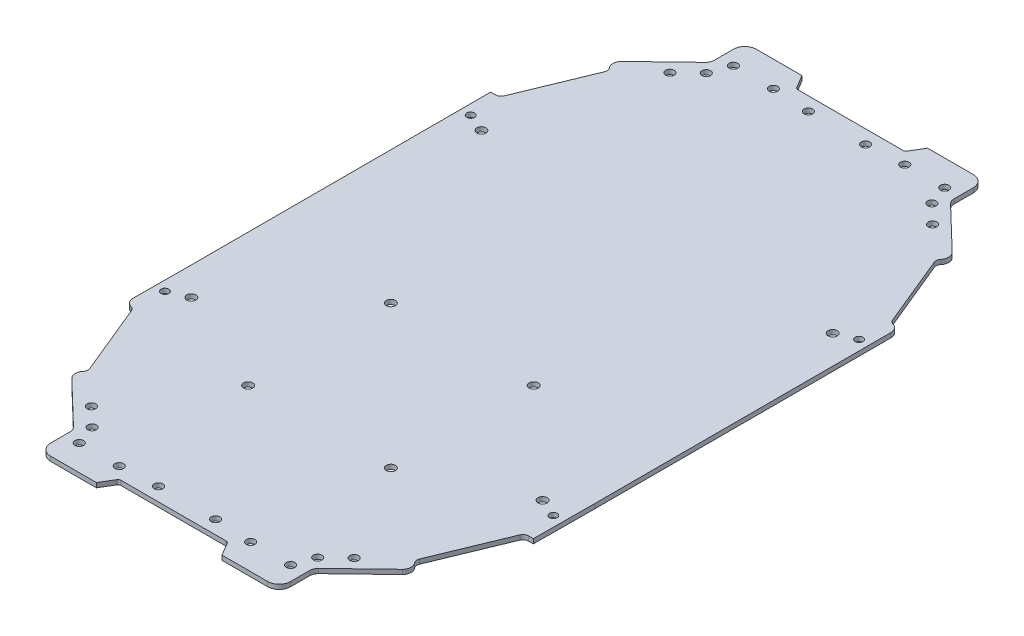
SolidWorks part; units mm, degrees
ref_plane "Front Plane" through (0, 0, 0) normal (0, 0, 1) x (1, 0, 0)
ref_plane "Top Plane" through (0, 0, 0) normal (0, 1, 0) x (1, 0, 0)
ref_plane "Right Plane" through (0, 0, 0) normal (1, 0, 0) x (0, 0, -1)
ref_plane "Plane1"
sketch "Sketch1" plane through (0, 0, 0) normal (0, 1, 0) x (-1, 0, 0)
  line L0 (59.7752, 259.0599) -> (56.7752, 264.0599)
  line L1 (56.7752, 264.0599) -> (36.7752, 264.0599)
  line L2 (36.7752, 264.0599) -> (36.7752, 252.0599)
  line L3 (36.7752, 252.0599) -> (18.7553, 234.7311)
  line L4 (18.7553, 234.7311) -> (21.5279, 231.8479)
  line L5 (21.5279, 231.8479) -> (10.2752, 204.5599)
  line L6 (10.2752, 204.5599) -> (7.2711, 204.5599)
  line L7 (7.2711, 204.5599) -> (7.1571, 183.0599)
  line L8 (7.1571, 183.0599) -> (7.1571, 76.6124)
  line L9 (7.1571, 76.6124) -> (10.1571, 76.6124)
  line L10 (10.1571, 76.6124) -> (21.4099, 49.3243)
  line L11 (21.4099, 49.3243) -> (18.6373, 46.4412)
  line L12 (18.6373, 46.4412) -> (36.6571, 29.1124)
  line L13 (36.6571, 29.1124) -> (36.6571, 17.1124)
  line L14 (36.6571, 17.1124) -> (56.6571, 17.1124)
  line L15 (56.6571, 17.1124) -> (59.6571, 22.1124)
  line L16 (59.6571, 22.1124) -> (78.6571, 22.1124)
  line L17 (78.6571, 22.1124) -> (97.6571, 22.1124)
  line L18 (97.6571, 22.1124) -> (100.6571, 17.1124)
  line L19 (100.6571, 17.1124) -> (120.6571, 17.1124)
  line L20 (120.6571, 17.1124) -> (120.6571, 29.1124)
  line L21 (120.6571, 29.1124) -> (138.677, 46.4412)
  line L22 (138.677, 46.4412) -> (135.9044, 49.3243)
  line L23 (135.9044, 49.3243) -> (147.1571, 76.6124)
  line L24 (147.1571, 76.6124) -> (150.1571, 76.6124)
  line L25 (150.1571, 76.6124) -> (150.1571, 183.0599)
  line L26 (150.1571, 183.0599) -> (150.2752, 204.5599)
  line L27 (150.2752, 204.5599) -> (147.2752, 204.5599)
  line L28 (147.2752, 204.5599) -> (136.0224, 231.8479)
  line L29 (136.0224, 231.8479) -> (138.795, 234.7311)
  line L30 (138.795, 234.7311) -> (120.7752, 252.0599)
  line L31 (120.7752, 252.0599) -> (120.7752, 264.0599)
  line L32 (120.7752, 264.0599) -> (100.7752, 264.0599)
  line L33 (100.7752, 264.0599) -> (97.7752, 259.0599)
  line L34 (97.7752, 259.0599) -> (78.6571, 259.0599)
  line L35 (78.6571, 259.0599) -> (59.7752, 259.0599)
  line L38 (78.6571, 259.0599) -> (78.6571, 22.1124) construction
  line L39 (150.1571, 183.0599) -> (7.1571, 183.0599) construction
  line L85 (91.8838, 199.6325) -> (91.9874, 199.5289)
  line L87 (95.3777, 196.1387) -> (95.4193, 196.097)
  circle A0 centre (55.6571, 26.1124) radius 1.5
  circle A1 centre (39.1571, 33.1124) radius 1.5
  circle A2 centre (53.6571, 208.0599) radius 1.6
  circle A3 centre (53.6571, 158.0599) radius 1.6
  circle A4 centre (17.1571, 89.8624) radius 1.6
  circle A5 centre (103.6571, 158.0599) radius 1.6
  circle A22 centre (41.7752, 255.0599) radius 1.5
  circle A23 centre (39.2752, 248.0599) radius 1.5
  circle A24 centre (10.7752, 194.0599) radius 1.35
  circle A25 centre (88.6571, 26.8624) radius 1.5
  circle A27 centre (115.6571, 26.1124) radius 1.5
  circle A28 centre (118.1571, 33.1124) radius 1.5
  circle A29 centre (140.1571, 89.8624) radius 1.6
  circle A30 centre (115.7752, 255.0599) radius 1.5
  circle A31 centre (88.7752, 254.3099) radius 1.5
  circle A32 centre (140.2752, 191.3099) radius 1.6
  circle A33 centre (146.7752, 194.0599) radius 1.35
  circle A53 centre (101.7752, 255.0599) radius 1.5
  circle A54 centre (118.2752, 248.0599) radius 1.5
  circle A55 centre (146.6571, 87.1124) radius 1.35
  circle A57 centre (101.6571, 26.1124) radius 1.5
  circle A69 centre (17.2752, 191.3099) radius 1.6
  circle A71 centre (55.7752, 255.0599) radius 1.5
  circle A73 centre (68.7752, 254.3099) radius 1.5
  circle A74 centre (10.6571, 87.1124) radius 1.35
  circle A76 centre (68.6571, 26.8624) radius 1.5
  circle A77 centre (41.6571, 26.1124) radius 1.5
  circle A82 centre (32.6571, 39.3624) radius 1.5
  circle A86 centre (124.7752, 241.8099) radius 1.5
  circle A87 centre (32.7752, 241.8099) radius 1.5
  circle A90 centre (103.6571, 208.0599) radius 1.6
  circle A91 centre (124.6571, 39.3624) radius 1.5
  point P41 (150.2161, 193.8099)
  dimension "D1" = 143
  dimension "D3" = 25
  dimension "D4" = 25
extrude "Extrusion1" add sketch "Sketch1" along normal blind 1.6
fillet "Fillet1" radius 1 4 edges at (-97.6571, 0.8, 22.1124) (-59.6571, 0.8, 22.1124) (-59.7752, 0.8, 259.0599) (-97.7752, 0.8, 259.0599)
fillet "Fillet2" radius 4 4 edges at (-120.6571, 0.8, 17.1124) (-36.6571, 0.8, 17.1124) (-120.7752, 0.8, 264.0599) (-36.7752, 0.8, 264.0599)
fillet "Fillet3" radius 3 4 edges at (-120.6571, 0.8, 29.1124) (-36.6571, 0.8, 29.1124) (-36.7752, 0.8, 252.0599) (-120.7752, 0.8, 252.0599)
fillet "Fillet4" radius 3 1 edges at (-138.795, 0.8, 234.7311)
fillet "Fillet5" radius 2 1 edges at (-136.0224, 0.8, 231.8479)
fillet "Fillet6" radius 2 1 edges at (-21.5279, 0.8, 231.8479)
fillet "Fillet7" radius 3 1 edges at (-18.7553, 0.8, 234.7311)
fillet "Fillet8" radius 3 2 edges at (-138.677, 0.8, 46.4412) (-18.6373, 0.8, 46.4412)
fillet "Fillet9" radius 2 2 edges at (-21.4099, 0.8, 49.3243) (-135.9044, 0.8, 49.3243)
fillet "Fillet10" radius 2 4 edges at (-10.1571, 0.8, 76.6124) (-10.2752, 0.8, 204.5599) (-147.2752, 0.8, 204.5599) (-147.1571, 0.8, 76.6124)
fillet "Fillet11" radius 3 2 edges at (-150.2752, 0.8, 204.5599) (-7.1571, 0.8, 76.6124)
